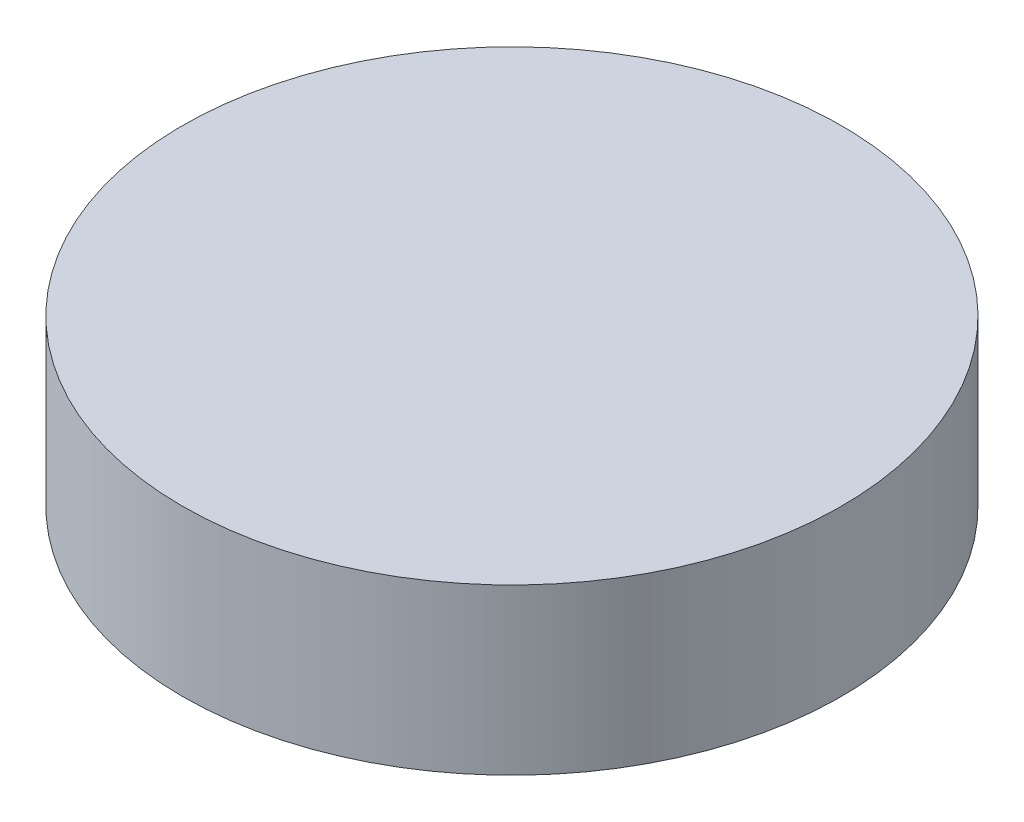
SolidWorks part; units mm, degrees
ref_plane "Front Plane" through (0, 0, 0) normal (0, 0, 1) x (1, 0, 0)
ref_plane "Top Plane" through (0, 0, 0) normal (0, 1, 0) x (1, 0, 0)
ref_plane "Right Plane" through (0, 0, 0) normal (1, 0, 0) x (0, 0, -1)
sketch "Sketch1" plane through (0, 0, 0) normal (0, 1, 0) x (1, 0, 0)
  circle A0 centre (0, 0) radius 200
extrude "Boss-Extrude1" add sketch "Sketch1" along normal blind 100
